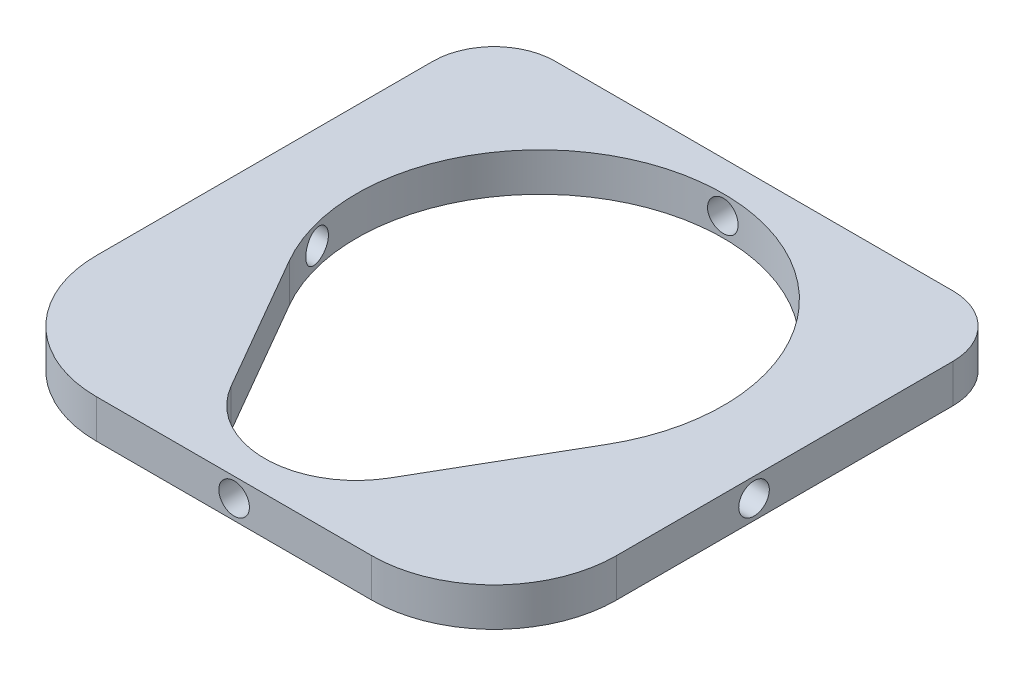
SolidWorks part; units mm, degrees
ref_plane "Front Plane" through (0, 0, 0) normal (0, 0, 1) x (1, 0, 0)
ref_plane "Top Plane" through (0, 0, 0) normal (0, 1, 0) x (1, 0, 0)
ref_plane "Right Plane" through (0, 0, 0) normal (1, 0, 0) x (0, 0, -1)
sketch "Sketch1" plane through (0, 0, 0) normal (0, 1, 0) x (1, 0, 0)
  line L1 (0, 0) -> (85, 0)
  line L2 (0, 0) -> (0, 85)
  line L3 (0, 85) -> (85, 85)
  line L4 (85, 0) -> (85, 85)
  dimension "D1" = 85
  dimension "D2" = 85
extrude "Boss-Extrude1" add sketch "Sketch1" along normal blind 6.3
sketch "Sketch2" plane through (0, 6.3, 0) normal (0, 1, 0) x (1, 0, 0)
  line L0 (0, 85) -> (85, 0) construction
  line L1 (42.5, 85) -> (42.5, 0) construction
  line L2 (85, 85) -> (0, 85) construction
  line L3 (0, 0) -> (85, 0) construction
  line L4 (16.5192, 35) -> (29.5096, 12.5)
  line L5 (55.4904, 12.5) -> (68.4808, 35)
  line L6 (0, 5) -> (85, 5) construction
  line L7 (0, 85) -> (0, 0) construction
  line L8 (85, 0) -> (85, 85) construction
  line L9 (0, 80) -> (85, 80) construction
  arc A0 (68.4808, 35) -> (16.5192, 35) centre (42.5, 50) ccw
  arc A1 (29.5096, 12.5) -> (55.4904, 12.5) centre (42.5, 20) ccw
  dimension "D1" = 30
  dimension "D3" = 15
  dimension "D2" = 30
  dimension "D4" = 5
  dimension "D5" = 5
extrude "Cut-Extrude1" cut sketch "Sketch2" against normal blind 10
sketch "Sketch3" plane through (0, 0, 0) normal (0, 0, 1) x (1, 0, 0)
  line L0 (0, 6.3) -> (85, 0) construction
  circle A0 centre (42.5, 3.15) radius 2.5
  dimension "D1" = 5
extrude "Cut-Extrude2" cut sketch "Sketch3" against normal through all
sketch "Sketch4" plane through (0, 0, 0) normal (-1, 0, 0) x (0, 0, 1)
  line L0 (-85, 6.3) -> (0, 0) construction
  circle A0 centre (-42.5, 3.15) radius 2.5
  dimension "D1" = 5
extrude "Cut-Extrude3" cut sketch "Sketch4" against normal through all
fillet "Fillet1" radius 20 2 edges at (85, 3.15, 0) (0, 3.15, 0)
fillet "Fillet2" radius 10 2 edges at (85, 3.15, -85) (0, 3.15, -85)
equation "\"D2@Sketch2\"=\"D1@Sketch2\""
equation "\"D3@Sketch2\"=\"D1@Sketch2\"/2"
